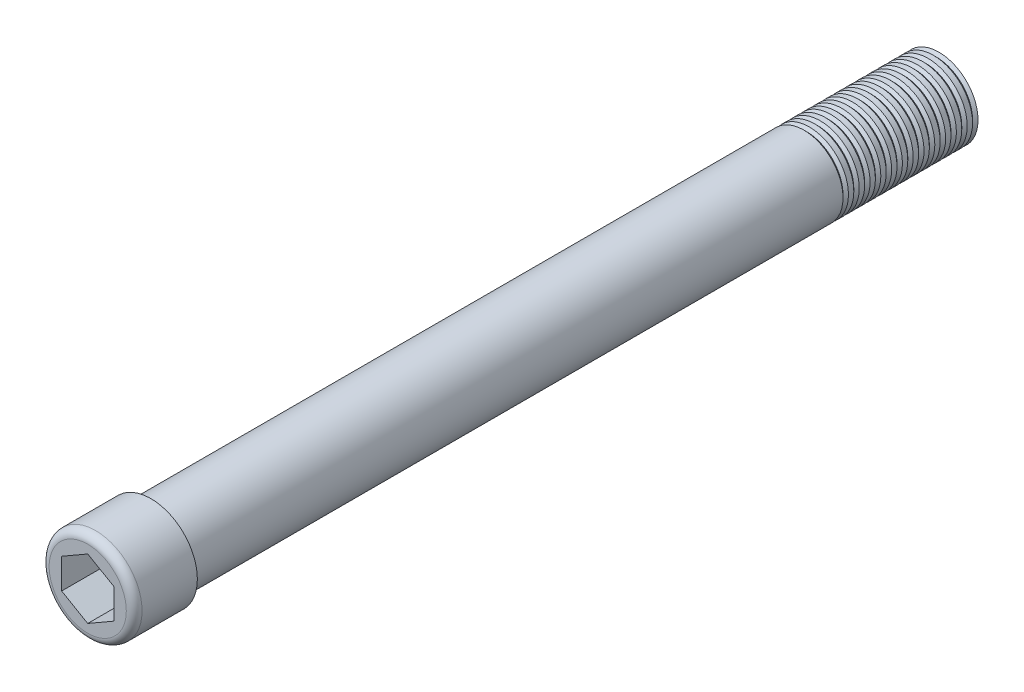
SolidWorks part; units mm, degrees
ref_plane "Front Plane" through (0, 0, 0) normal (0, 0, 1) x (1, 0, 0)
ref_plane "Top Plane" through (0, 0, 0) normal (0, 1, 0) x (1, 0, 0)
ref_plane "Right Plane" through (0, 0, 0) normal (1, 0, 0) x (0, 0, -1)
sketch "Sketch1" plane through (0, 0, 0) normal (0, 0, 1) x (1, 0, 0)
  circle A0 centre (0, 0) radius 6.3
  dimension "D1" = 12.6
extrude "Extrude1" add sketch "Sketch1" along normal blind 127
sketch "Sketch2" plane through (0, 0, 127) normal (0, 0, 1) x (1, 0, 0)
  circle A0 centre (0, 0) radius 7.4862
  dimension "D1" = 14.9724
extrude "Extrude2" add sketch "Sketch2" along normal blind 10.18
fillet "Fillet1" radius 1.27 1 edges at (7.4862, 0, 137.18)
sketch "Sketch3" plane through (0, 0, 137.18) normal (0, 0, 1) x (1, 0, 0)
  line L1 (4.2026, 2.4239) -> (0.0021, 4.8515)
  line L2 (0.0021, 4.8515) -> (-4.2005, 2.4276)
  line L3 (-4.2005, 2.4276) -> (-4.2026, -2.4239)
  line L4 (-4.2026, -2.4239) -> (-0.0021, -4.8515)
  line L5 (-0.0021, -4.8515) -> (4.2005, -2.4276)
  line L6 (4.2005, -2.4276) -> (4.2026, 2.4239)
  circle A0 centre (0, 0) radius 4.2015 construction
extrude "Cut-Extrude1" cut sketch "Sketch3" against normal blind 10.18
sketch "Sketch4" plane through (0, 0, 0) normal (0, 1, 0) x (1, 0, 0)
  line L0 (-6.3, 0) -> (-5.8613, -0.4387)
  line L1 (-5.8613, -0.4387) -> (-6.3, -0.8774)
  line L2 (-6.3, -0.8774) -> (-6.7387, -0.4387)
  line L3 (-6.7387, -0.4387) -> (-6.3, 0)
revolve "Cut-Revolve1" cut sketch "Sketch4" angle 360 about axis through (0, 0, 127) along (0, 0, -1)
pattern_linear "LPattern1" count 13 spacing 1.74 along (0, 0, 1) of "Cut-Revolve1"
